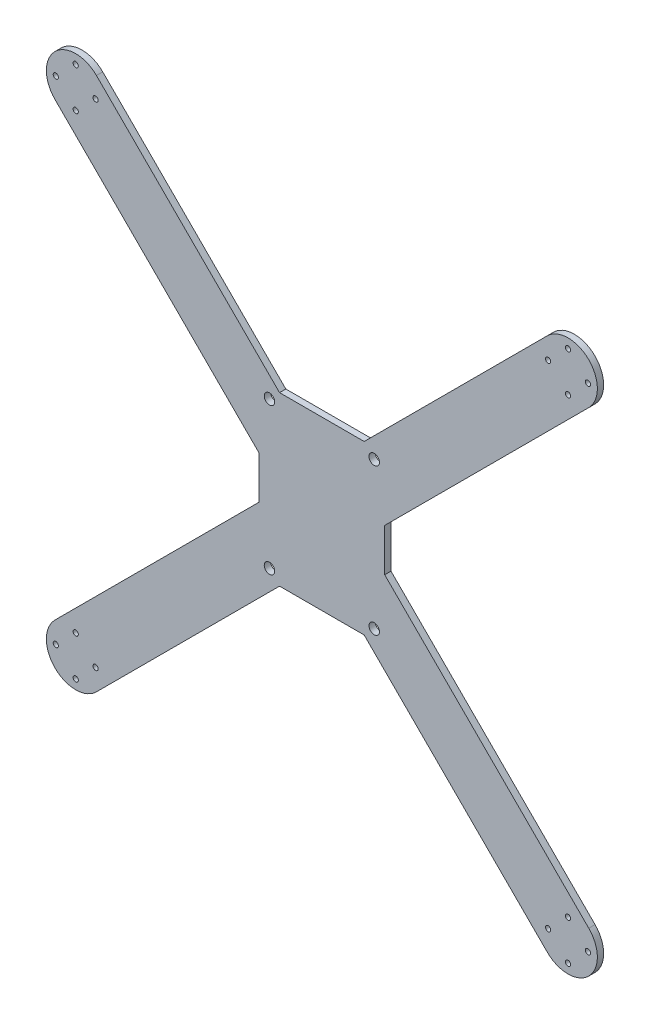
SolidWorks part; units mm, degrees
material "Custom Plastic"
ref_plane "Front Plane" through (0, 0, 0) normal (0, 0, 1) x (1, 0, 0)
ref_plane "Top Plane" through (0, 0, 0) normal (0, 1, 0) x (1, 0, 0)
ref_plane "Right Plane" through (0, 0, 0) normal (1, 0, 0) x (0, 0, -1)
sketch "Sketch1" plane through (0, 0, 0) normal (0, 0, 1) x (1, 0, 0)
  line L0 (117.5, 117.5) -> (-117.5, 117.5) construction
  line L1 (-117.5, 117.5) -> (117.5, -117.5) construction
  line L2 (117.5, -117.5) -> (-117.5, -117.5) construction
  line L3 (-117.5, -117.5) -> (117.5, 117.5) construction
  line L4 (117.5, 117.5) -> (117.5, -117.5) construction
  line L5 (-117.5, 117.5) -> (-117.5, -117.5) construction
  line L6 (0, 117.5) -> (0, -117.5) construction
  line L7 (20.201, 40) -> (-20.201, 40)
  line L8 (-30, 40) -> (30, 40) construction
  line L9 (-20.201, 40) -> (-107.6005, 127.3995)
  line L10 (-127.3995, 107.6005) -> (-30, 10.201)
  line L11 (-117.5, 0) -> (117.5, 0) construction
  line L12 (-30, 10.201) -> (-30, -10.201)
  line L13 (30, 40) -> (30, -40) construction
  line L14 (30, -40) -> (-30, -40) construction
  line L15 (-30, -40) -> (-30, 40) construction
  line L16 (30, 40) -> (-30, -40) construction
  line L18 (-127.3995, -107.6005) -> (-30, -10.201)
  line L20 (-20.201, -40) -> (-107.6005, -127.3995)
  line L21 (20.201, -40) -> (-20.201, -40)
  line L22 (20.201, -40) -> (107.6005, -127.3995)
  line L23 (127.3995, -107.6005) -> (30, -10.201)
  line L24 (30, 10.201) -> (30, -10.201)
  line L25 (127.3995, 107.6005) -> (30, 10.201)
  line L26 (20.201, 40) -> (107.6005, 127.3995)
  arc A0 (-107.6005, 127.3995) -> (-127.3995, 107.6005) centre (-117.5, 117.5) ccw
  arc A12 (-107.6005, -127.3995) -> (-127.3995, -107.6005) centre (-117.5, -117.5) cw
  arc A16 (107.6005, -127.3995) -> (127.3995, -107.6005) centre (117.5, -117.5) ccw
  arc A24 (107.6005, 127.3995) -> (127.3995, 107.6005) centre (117.5, 117.5) cw
  point P3 (0, 0)
  point P18 (0, 0)
  point P33 (-117.5, 117.5)
  point P34 (-30, 0)
  point P65 (0, -40)
  point P80 (0, 40)
  dimension "D3" = 14
  dimension "D1" = 235
  dimension "D2" = 235
  dimension "D4" = 60
  dimension "D5" = 80
  dimension "D6" = 28
extrude "Boss-Extrude1" add sketch "Sketch1" against normal blind 3
sketch "Sketch4" plane through (0, 0, 0) normal (0, 0, 1) x (1, 0, 0)
  line L0 (0, 0) -> (0, 40) construction
  line L1 (20.201, 40) -> (-20.201, 40) construction
  line L2 (0, 0) -> (-30, 0) construction
  line L3 (-30, 10.201) -> (-30, -10.201) construction
  line L4 (-30, 0) -> (-30, 10.201) construction
  line L5 (-30, 10.201) -> (-127.3995, 107.6005) construction
  line L6 (-20.201, 40) -> (-107.6005, 127.3995) construction
  line L7 (-107.6005, 127.3995) -> (-127.3995, 107.6005) construction
  line L8 (-117.5, 117.5) -> (-108, 117.5) construction
  line L9 (-117.5, 127) -> (-117.5, 117.5) construction
  circle A0 centre (-108, 117.5) radius 1.25
  circle A1 centre (-117.5, 108) radius 1.25
  circle A2 centre (-127, 117.5) radius 1.25
  circle A3 centre (-117.5, 127) radius 1.25
  circle A4 centre (-25, 35) radius 2.5
  circle A5 centre (-117.5, -108) radius 1.25
  circle A6 centre (-127, -117.5) radius 1.25
  circle A7 centre (-117.5, -127) radius 1.25
  circle A8 centre (-108, -117.5) radius 1.25
  circle A9 centre (-25, -35) radius 2.5
  circle A10 centre (108, -117.5) radius 1.25
  circle A11 centre (117.5, -127) radius 1.25
  circle A12 centre (127, -117.5) radius 1.25
  circle A13 centre (117.5, -108) radius 1.25
  circle A14 centre (117.5, 108) radius 1.25
  circle A15 centre (127, 117.5) radius 1.25
  circle A16 centre (117.5, 127) radius 1.25
  circle A17 centre (108, 117.5) radius 1.25
  circle A18 centre (25, -35) radius 2.5
  circle A19 centre (25, 35) radius 2.5
  point P27 (-117.5, 117.5)
  dimension "D1" = 2.5
  dimension "D6" = 5
  dimension "D2" = 9.5
  dimension "D4" = 90
  dimension "D5" = 9.5
  dimension "D7" = 5
  dimension "D8" = 5
  dimension "D3" = 4
extrude "Cut-Extrude1" cut sketch "Sketch4" against normal blind 3
